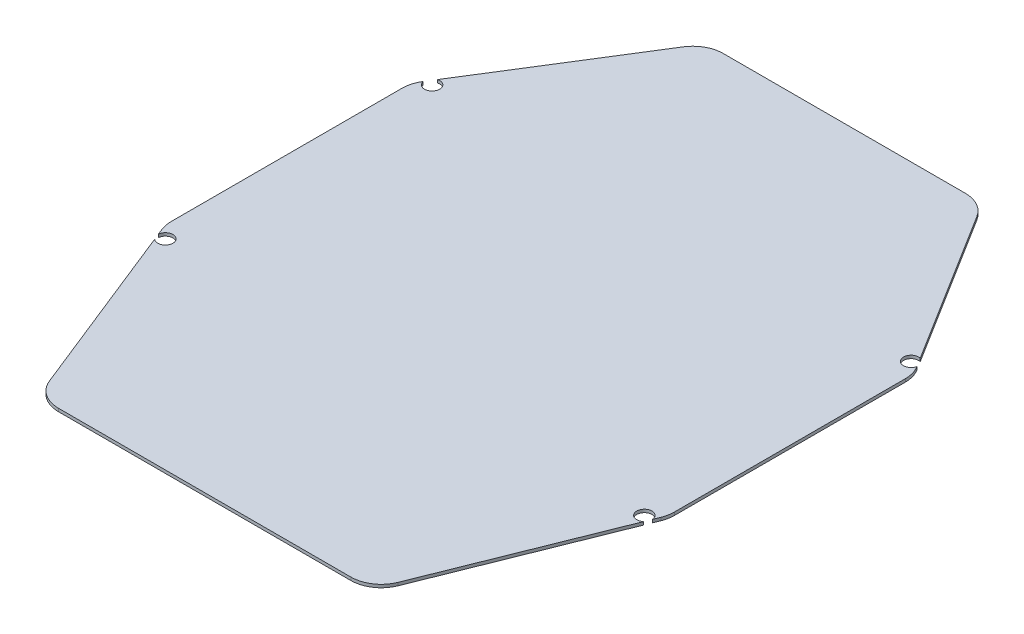
SolidWorks part; units mm, degrees
ref_plane "Front Plane" through (0, 0, 0) normal (0, 0, 1) x (1, 0, 0)
ref_plane "Top Plane" through (0, 0, 0) normal (0, 1, 0) x (1, 0, 0)
ref_plane "Right Plane" through (0, 0, 0) normal (1, 0, 0) x (0, 0, -1)
sketch "Sketch1" plane through (0, 0, 0) normal (0, 1, 0) x (1, 0, 0)
  line L0 (83, -33.5742) -> (83, 42.632)
  line L1 (81.48, 47.932) -> (48.4375, 100.8)
  line L2 (39.9575, 105.5) -> (-39.9575, 105.5)
  line L3 (-48.4375, 100.8) -> (-81.48, 47.932)
  line L4 (-83, 42.632) -> (-83, -33.5742)
  line L5 (-82.2848, -37.2881) -> (-57.5144, -99.2139)
  line L6 (-48.2297, -105.5) -> (48.2297, -105.5)
  line L7 (57.5144, -99.2139) -> (82.2848, -37.2881)
  arc A0 (83, 42.632) -> (81.48, 47.932) centre (73, 42.632) ccw
  arc A1 (48.4375, 100.8) -> (39.9575, 105.5) centre (39.9575, 95.5) ccw
  arc A2 (-39.9575, 105.5) -> (-48.4375, 100.8) centre (-39.9575, 95.5) ccw
  arc A3 (-81.48, 47.932) -> (-83, 42.632) centre (-73, 42.632) ccw
  arc A4 (-83, -33.5742) -> (-82.2848, -37.2881) centre (-73, -33.5742) ccw
  arc A5 (-57.5144, -99.2139) -> (-48.2297, -105.5) centre (-48.2297, -95.5) ccw
  arc A6 (48.2297, -105.5) -> (57.5144, -99.2139) centre (48.2297, -95.5) ccw
  arc A7 (82.2848, -37.2881) -> (83, -33.5742) centre (73, -33.5742) ccw
extrude "Boss-Extrude1" add sketch "Sketch1" along normal blind 1
sketch "Sketch2" plane through (0, 1, 0) normal (0, 1, 0) x (1, 0, 0)
  line L0 (83, -33.5742) -> (-83, -33.5742) construction
  line L1 (-83, 4.5289) -> (83, 4.5289) construction
  line L2 (-83, 42.632) -> (-83, -33.5742) construction
  line L3 (83, -33.5742) -> (83, 42.632) construction
  line L4 (0, -33.5742) -> (0, 4.5289) construction
  circle A0 centre (79, 48.5289) radius 2.5
  circle A1 centre (79, -39.4711) radius 2.5
  circle A2 centre (-79, 48.5289) radius 2.5
  circle A3 centre (-79, -39.4711) radius 2.5
  dimension "D1" = 5
  dimension "D2" = 5
  dimension "D3" = 5
  dimension "D4" = 5
  dimension "D5" = 158
  dimension "D6" = 79
  dimension "D7" = 79
  dimension "D8" = 79
  dimension "D9" = 44
  dimension "D10" = 44
  dimension "D11" = 44
  dimension "D12" = 44
extrude "Cut-Extrude1" cut sketch "Sketch2" against normal blind 1
